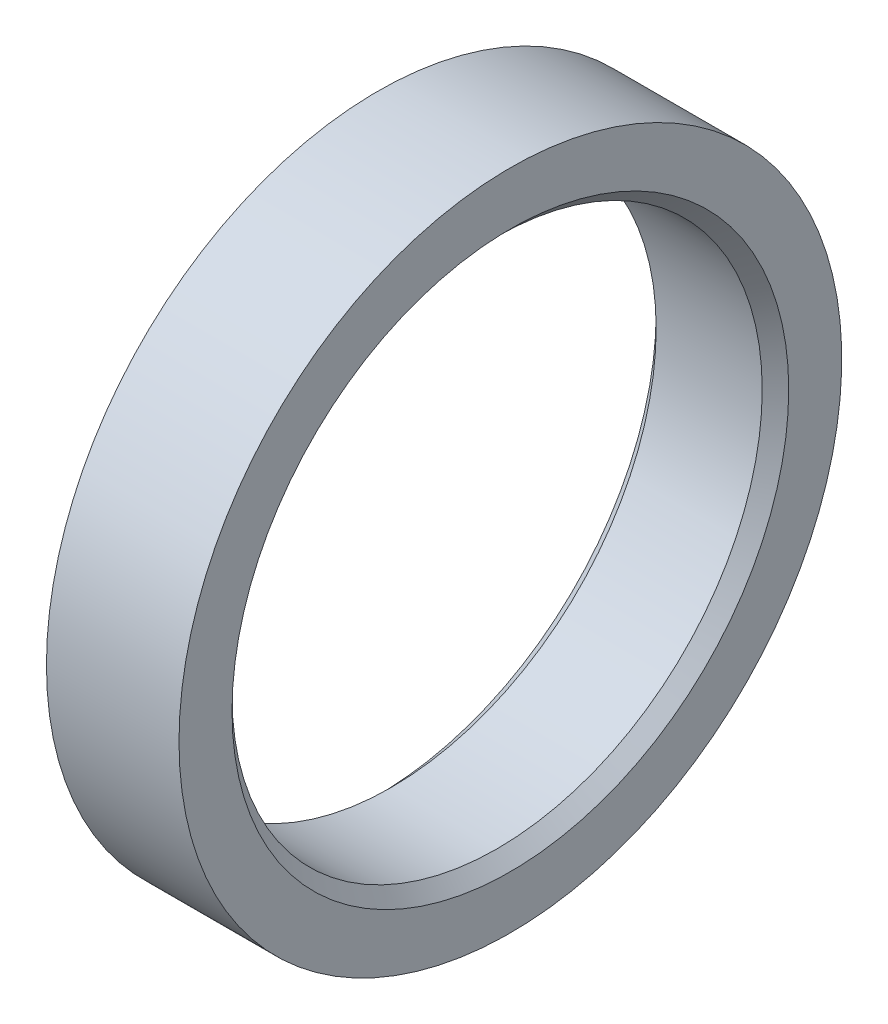
SolidWorks part; units mm, degrees
ref_plane "Přední rovina" through (0, 0, 0) normal (0, 0, 1) x (1, 0, 0)
ref_plane "Vrchní rovina" through (0, 0, 0) normal (0, 1, 0) x (1, 0, 0)
ref_plane "Pravá rovina" through (0, 0, 0) normal (1, 0, 0) x (0, 0, -1)
sketch "Skica1" plane through (0, 0, 0) normal (0, 0, 1) x (1, 0, 0)
  line L0 (0, 0) -> (15.1181, 0) construction
  line L1 (0, 20) -> (0, 25)
  line L2 (0, 25) -> (10, 25)
  line L3 (10, 25) -> (10, 20)
  line L4 (0, 20) -> (10, 20)
  point P3 (13.2283, 20)
  point P8 (0, 0)
  dimension "D1" = 50
  dimension "D2" = 40
  dimension "D3" = 10
revolve "Rotovat1" add sketch "Skica1" angle 360 about L0
chamfer "Zkosení1" distance 1 angle 45 2 edges at (0, 0, 20) (10, 0, 20)
